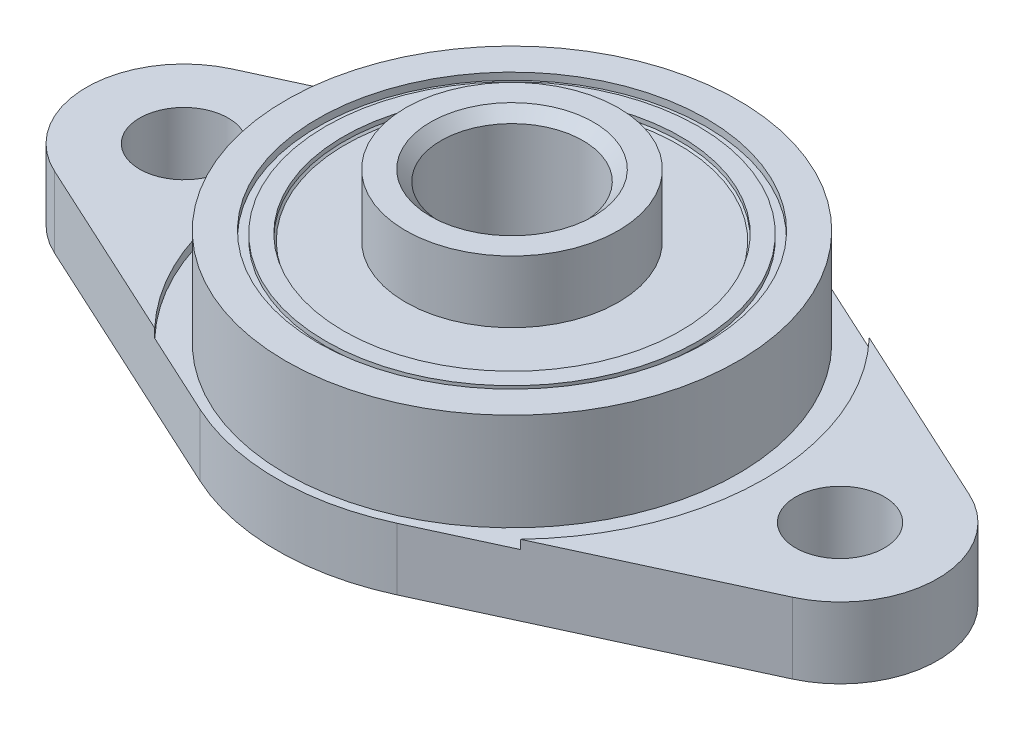
SolidWorks part; units mm, degrees
ref_plane "Front Plane" through (0, 0, 0) normal (0, 0, 1) x (1, 0, 0)
ref_plane "Top Plane" through (0, 0, 0) normal (0, 1, 0) x (1, 0, 0)
ref_plane "Right Plane" through (0, 0, 0) normal (1, 0, 0) x (0, 0, -1)
sketch "Sketch2" plane through (0, 0, 0) normal (0, 1, 0) x (1, 0, 0)
  line L0 (0, 15.7574) -> (0, -15.7574) construction
  line L1 (-5.5507, 12.0313) -> (-20.8041, 4.9941)
  line L2 (-37.1587, 0) -> (38.3179, 0) construction
  line L3 (5.5507, 12.0313) -> (20.8041, 4.9941)
  line L4 (5.5507, -12.0313) -> (20.8041, -4.9941)
  line L5 (-5.5507, -12.0313) -> (-20.8041, -4.9941)
  circle A0 centre (-18.5, 0) radius 2.5
  arc A1 (-20.8041, 4.9941) -> (-20.8041, -4.9941) centre (-18.5, 0) ccw
  arc A2 (5.5507, 12.0313) -> (-5.5507, 12.0313) centre (0, 0) ccw
  circle A3 centre (18.5, 0) radius 2.5
  arc A4 (20.8041, 4.9941) -> (20.8041, -4.9941) centre (18.5, 0) cw
  arc A5 (-5.5507, -12.0313) -> (5.5507, -12.0313) centre (0, 0) ccw
  dimension "D1" = 2.5
  dimension "D2" = 5.5
  dimension "D3" = 26.5
  dimension "D4" = 18.5
extrude "Boss-Extrude1" add sketch "Sketch2" along normal blind 4
sketch "Sketch3" plane through (0, 4, 0) normal (0, 1, 0) x (1, 0, 0)
  circle A0 centre (0, 0) radius 14.25
  dimension "D1" = 14.25
extrude "Cut-Extrude1" cut sketch "Sketch3" against normal blind 0.5
sketch "Sketch4" plane through (0, 3.5, 0) normal (0, 1, 0) x (1, 0, 0)
  circle A0 centre (0, 0) radius 12.75
  dimension "D1" = 12.75
extrude "Boss-Extrude2" add sketch "Sketch4" along normal blind 5.5
sketch "Sketch5" plane through (0, 0, 0) normal (0, -1, 0) x (1, 0, 0)
  line L8 (4.8385, -10.4877) -> (20.0919, -3.4505)
  line L9 (20.0919, 3.4505) -> (4.8385, 10.4877)
  line L10 (-4.8385, 10.4877) -> (-20.0919, 3.4505)
  line L11 (-20.0919, -3.4505) -> (-4.8385, -10.4877)
  line L12 (4.8385, -10.4877) -> (16.4814, -5.1162)
  line L13 (16.4814, 5.1162) -> (4.8385, 10.4877)
  line L14 (-4.8385, 10.4877) -> (-16.4814, 5.1162)
  line L15 (-16.4814, -5.1162) -> (-4.8385, -10.4877)
  arc A4 (-16.4814, -5.1162) -> (-16.4814, 5.1162) centre (-18.5, 0) ccw
  arc A5 (16.4814, 5.1162) -> (16.4814, -5.1162) centre (18.5, 0) ccw
  arc A8 (-4.8385, -10.4877) -> (4.8385, -10.4877) centre (0, 0) ccw
  arc A9 (20.0919, -3.4505) -> (20.0919, 3.4505) centre (18.5, 0) ccw
  arc A10 (4.8385, 10.4877) -> (-4.8385, 10.4877) centre (0, 0) ccw
  arc A11 (-20.0919, 3.4505) -> (-20.0919, -3.4505) centre (-18.5, 0) ccw
  arc A12 (-4.8385, -10.4877) -> (4.8385, -10.4877) centre (0, 0) ccw
  arc A14 (4.8385, 10.4877) -> (-4.8385, 10.4877) centre (0, 0) ccw
  dimension "5.5" = 5.5
  dimension "D1" = 1.7
extrude "Cut-Extrude2" cut sketch "Sketch5" against normal blind 0.5
sketch "Sketch6" plane through (0, 9, 0) normal (0, 1, 0) x (1, 0, 0)
  circle A0 centre (0, 0) radius 10.95
  dimension "D1" = 21.9
extrude "Cut-Extrude3" cut sketch "Sketch6" against normal blind 0.4
sketch "Sketch7" plane through (0, 8.6, 0) normal (0, 1, 0) x (1, 0, 0)
  circle A0 centre (0, 0) radius 10.5
  point P3 (0, 0)
  dimension "D1" = 10.5
extrude "Boss-Extrude3" add sketch "Sketch7" along normal blind 0.25
sketch "Sketch8" plane through (0, 8.85, 0) normal (0, 1, 0) x (1, 0, 0)
  circle A0 centre (0, 0) radius 9.5
  dimension "D1" = 19
extrude "Cut-Extrude4" cut sketch "Sketch8" against normal blind 0.35
sketch "Sketch9" plane through (0, 0.5, 0) normal (0, -1, 0) x (1, 0, 0)
  circle A0 centre (0, 0) radius 10.5
  dimension "D1" = 21
extrude "Boss-Extrude4" add sketch "Sketch9" along normal blind 0.25
sketch "Sketch10" plane through (0, 0.25, 0) normal (0, -1, 0) x (1, 0, 0)
  circle A0 centre (0, 0) radius 9.5
  dimension "D1" = 19
extrude "Cut-Extrude5" cut sketch "Sketch10" against normal blind 0.35
sketch "Sketch11" plane through (0, 0.6, 0) normal (0, -1, 0) x (1, 0, 0)
  circle A0 centre (0, 0) radius 6
  dimension "D1" = 12
extrude "Boss-Extrude5" add sketch "Sketch11" along normal blind 0.35
sketch "Sketch12" plane through (0, 8.5, 0) normal (0, 1, 0) x (1, 0, 0)
  circle A0 centre (0, 0) radius 6
  dimension "D1" = 12
extrude "Boss-Extrude6" add sketch "Sketch12" along normal blind 3.5
sketch "Sketch13" plane through (0, 12, 0) normal (0, 1, 0) x (1, 0, 0)
  circle A0 centre (0, 0) radius 4
  dimension "D1" = 4
extrude "Cut-Extrude6" cut sketch "Sketch13" against normal through all both and the other way through all
chamfer "Chamfer1" distance 0.6 angle 45 1 edges at (0, 12, 4)
chamfer "Chamfer2" distance 0.6 angle 45 1 edges at (0, 0.25, -4)
chamfer "Chamfer3" distance 0.1 angle 45 2 edges at (0, 0.6, -9.5) (0, 8.5, 9.5)
